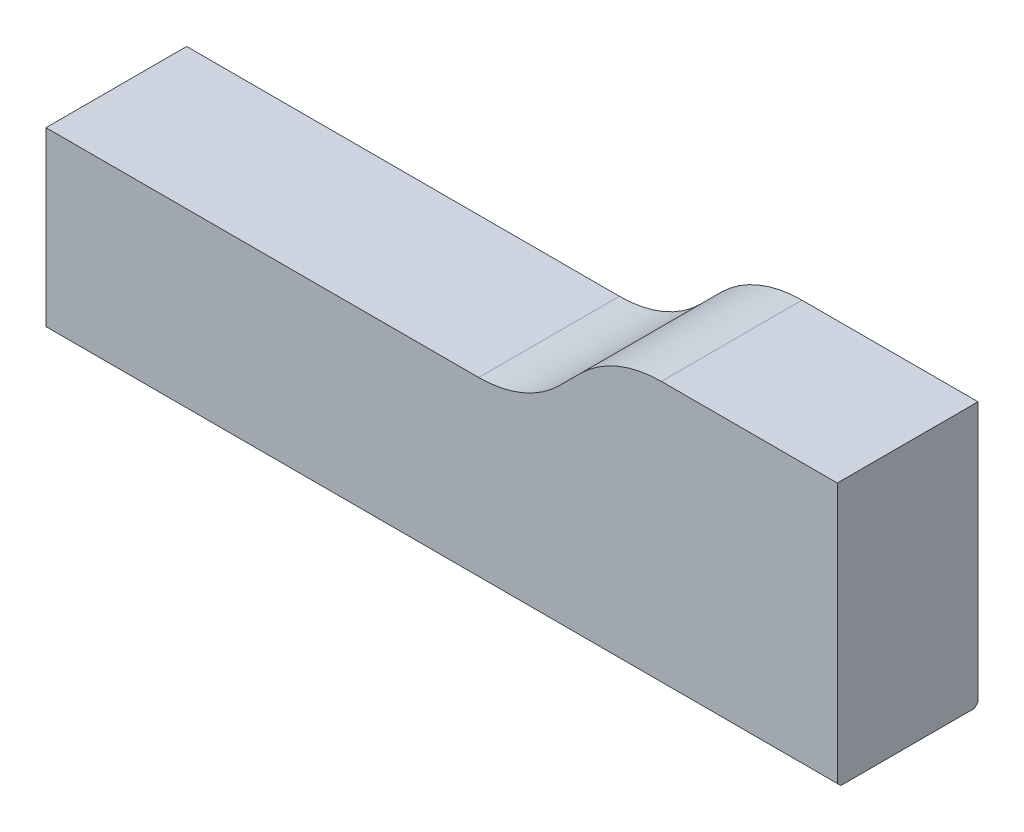
SolidWorks part; units mm, degrees
ref_plane "Front Plane" through (0, 0, 0) normal (0, 0, 1) x (1, 0, 0)
ref_plane "Top Plane" through (0, 0, 0) normal (0, 1, 0) x (1, 0, 0)
ref_plane "Right Plane" through (0, 0, 0) normal (1, 0, 0) x (0, 0, -1)
sketch "Sketch1" plane through (0, 0, 0) normal (0, 0, 1) x (1, 0, 0)
  line L0 (-1.561, 4.3659) -> (3.439, 9.3659)
  line L1 (-28.861, 4.3659) -> (-1.561, 4.3659)
  line L2 (-28.861, 4.3659) -> (-28.861, -5.6341)
  line L3 (-28.861, -5.6341) -> (16.139, -5.6341)
  line L4 (16.139, 9.3659) -> (16.139, -5.6341)
  line L7 (16.139, 9.3659) -> (3.439, 9.3659)
  dimension "D1" = 10
  dimension "D2" = 45
  dimension "D3" = 5
  dimension "D4" = 135
  dimension "D5" = 27.3
extrude "Boss-Extrude1" add sketch "Sketch1" along normal blind 8
fillet "Fillet1" radius 6.5 2 edges at (3.439, 9.3659, 4) (-1.561, 4.3659, 4)
chamfer "Chamfer1" distance 0.2 angle 45 2 edges at (-6.361, -5.6341, 8) (-6.361, -5.6341, 0)
hole_wizard "M3 Tapped Hole1" positions "Sketch4" profile "Sketch5" tap size "M3" standard "ISO"
sketch "Sketch4" plane through (0, -5.6341, 0) normal (0, -1, 0) x (-1, 0, 0)
  line L0 (28.861, -7.8) -> (28.861, -0.2) construction
  point P0 (21.361, -4)
  point P2 (-8.639, -4)
  point P7 (28.861, -4)
  dimension "D1" = 7.5
  dimension "D2" = 37.5
sketch "Sketch5" plane through (-21.361, -5.6341, 4) normal (1, 0, 0) x (0, 0, -1)
  line L0 (0, 0) -> (0, 6.7511)
  line L1 (0, 6.7511) -> (1.25, 6)
  line L2 (1.25, 6) -> (1.25, 0)
  line L5 (1.25, 0) -> (0, 0)
  line L10 (0, 6.7511) -> (-1.25, 6) construction
  line L11 (0, -6.35) -> (0, 107.95) construction
  dimension "Tap Drill Dia." = 2.5
  dimension "Tap Drill Depth" = 6
  dimension "Drill Angle" = 118
cosmetic thread "Hole Thread1" parameters "D1"=6, "D2"=3
cosmetic thread "Hole Thread2" parameters "D1"=6, "D2"=3
